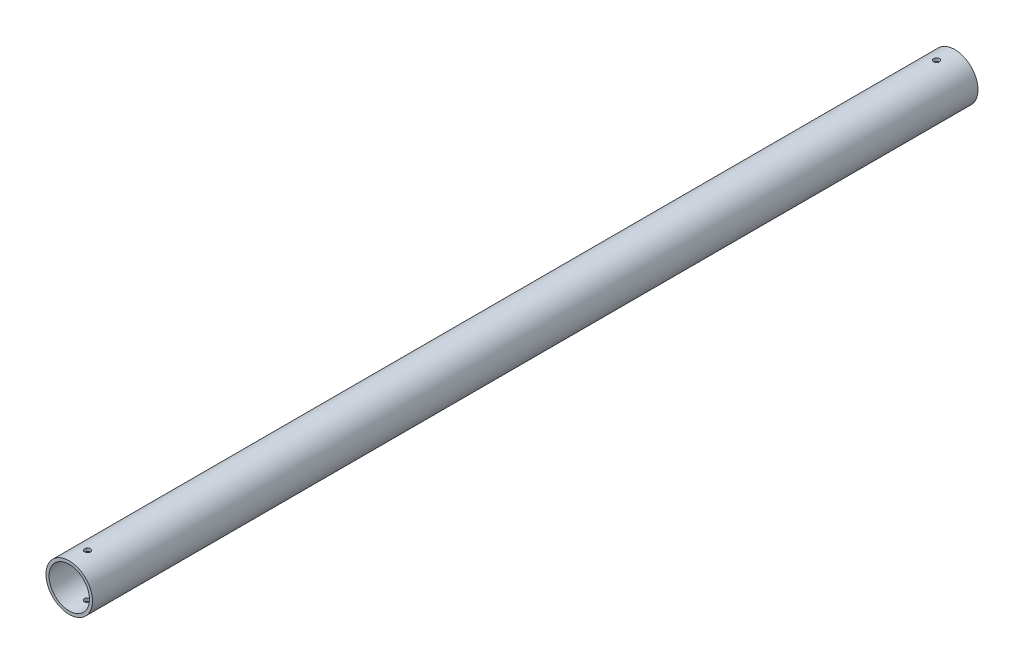
SolidWorks part; units mm, degrees
material "6063-T6, Rod (SS)"
ref_plane "Front Plane" through (0, 0, 0) normal (0, 0, 1) x (1, 0, 0)
ref_plane "Top Plane" through (0, 0, 0) normal (0, 1, 0) x (1, 0, 0)
ref_plane "Right Plane" through (0, 0, 0) normal (1, 0, 0) x (0, 0, -1)
sketch "Sketch1" plane through (0, 0, 0) normal (0, 0, 1) x (1, 0, 0)
  circle A0 centre (0, 0) radius 12.7
  circle A1 centre (0, 0) radius 11.049
  dimension "D1" = 25.4
  dimension "D2" = 22.098
extrude "Boss-Extrude1" add sketch "Sketch1" along normal mid plane 484
sketch "Sketch2" plane through (0, 0, 0) normal (0, 1, 0) x (1, 0, 0)
  line L0 (-12.7, -242) -> (12.7, -242) construction
  line L1 (-12.7, -232) -> (12.7, -232) construction
  line L2 (-12.7, 242) -> (-12.7, -242) construction
  line L3 (12.7, -242) -> (12.7, 242) construction
  circle A0 centre (0, -232) radius 1.6
  dimension "D1" = 3.2
  dimension "D2" = 10
extrude "Cut-Extrude1" cut sketch "Sketch2" against normal through all both and the other way through all
mirror "Mirror1" about plane through (0, 0, 0) normal (0, 0, 1) of "Cut-Extrude1"
